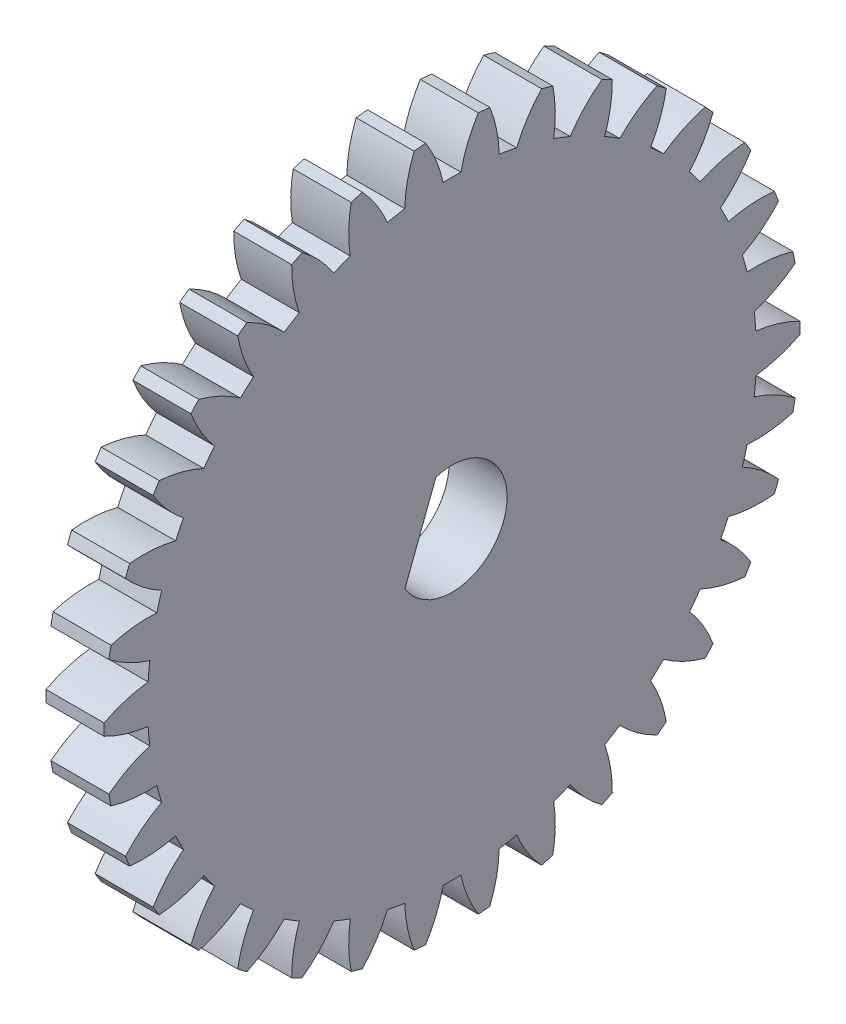
SolidWorks part; units mm, degrees
ref_plane "Plane1" through (0, 0, 0) normal (0, 0, 1) x (1, 0, 0)
ref_plane "Plane2" through (0, 0, 0) normal (0, 1, 0) x (1, 0, 0)
ref_plane "Plane3" through (0, 0, 0) normal (1, 0, 0) x (0, 0, -1)
sketch "HoldingSke" plane through (0, 0, 0) normal (0, 1, 0) x (1, 0, 0)
  line L0 (0, 0) -> (0.829, -0.5592)
  line L1 (-15, 0) -> (100, 0) construction
  line L2 (0, 0) -> (-2.1039, 2.3779)
  line L3 (0, 0) -> (-11.863, 4.5341)
  line L4 (0, 0) -> (7.1596, 4.8292)
  line L5 (0, 0) -> (-46.8476, -17.4728)
  line L6 (0, 0) -> (-2.4869, -1.6779)
  line L7 (-2.1039, 2.3779) -> (8.6586, 51.206)
  line L8 (-76.2, 54.61) -> (-75.7, 54.61)
  line L9 (-71.009, 38.7566) -> (-53.1078, 45.2721)
  line L10 (-76.2, 71.12) -> (104.1128, 71.12)
  line L11 (0, 0) -> (-3, 0)
  line L12 (-76.2, 101.6) -> (-76.162, 101.6)
  line L13 (24.9733, 27.94) -> (52.9518, 28.4284)
  line L14 (24.9733, 27.94) -> (24.9743, 27.94)
  line L15 (24.9733, 27.94) -> (100.4006, 29.5858)
  line L16 (-63.627, -1) -> (-12.827, -1)
  circle A0 centre (0, 0) radius 1.5
  circle A1 centre (0, 0) radius 15.749
  circle A2 centre (0, 0) radius 37.5
  circle A3 centre (0, 0) radius 1.5
  dimension "MHD" = 31.498
  dimension "Hub_dia" = 75
  dimension "Bore" = 3
  dimension "MBD" = 3
  dimension "Num_teeth" = 34
  dimension "Pitch" = 1
  dimension "Overall_len" = 50
  dimension "Show_teeth" = 34
  dimension "Thickness" = 3
  dimension "OAL" = 50.0002
  dimension "T_dim" = 0.5
  dimension "Ap" = 20
  dimension "H" = 19.05
  dimension "Pitch_radius" = 180.3128
  dimension "Width" = 3
  dimension "Backlash" = 0.038
  dimension "Addendum_fac" = 1
  dimension "Dedendum_fac" = 1.25
  dimension "Clearance_fac" = 0.25
  dimension "Dedendum_add" = 0.001
  dimension "Module" = 1
sketch "BasProSke" plane through (0, 0, 0) normal (0, 1, 0) x (1, 0, 0)
  line L0 (-10, 0) -> (60, 0) construction
  line L1 (0, 0) -> (0, 18)
  line L2 (0, 0) -> (3, 0)
  line L3 (3, 0) -> (3, 18)
  line L4 (3, 18) -> (0, 18)
  dimension "Thickness" = 3
  dimension "Diameter" = 36
revolve "Base-Revolve" add sketch "BasProSke" angle 360 about L0
sketch "TooCutSke" plane through (0, 0, 0) normal (1, 0, 0) x (0, 0, -1)
  line L1 (0, 0) -> (0, 107) construction
  line L2 (0, 0) -> (-0.8516, 16.9787) construction
  line L3 (0, 0) -> (-3.1343, 33.8247) construction
  line L4 (-0.8516, 16.9787) -> (-1.5672, 16.9124) construction
  arc A0 (0.4581, 15.7423) -> (-0.4581, 15.7423) centre (0, 0) ccw
  arc A1 (1.3773, 17.9727) -> (-1.3773, 17.9727) centre (0, 0) ccw
  circle A2 centre (0, 0) radius 17 construction
  circle A3 centre (0, 0) radius 15.9748 construction
  arc A4 (-0.4581, 15.7423) -> (-1.3773, 17.9727) centre (-7.1051, 14.3077) ccw
  arc A5 (1.3773, 17.9727) -> (0.4581, 15.7423) centre (7.1051, 14.3077) ccw
  dimension "Root_dia" = 31.498
  dimension "Overcut_dia" = 36.0508
  dimension "Pitch_dia" = 34
  dimension "Base_dia" = 31.9495
  dimension "Flank_rad" = 6.8
  dimension "Half_ang" = 5.294
  dimension "Half_CT" = 0.7186
extrude "ToothCut" cut sketch "TooCutSke" along normal through all
fillet "Breaks" [suppressed] radius 0.02
fillet "RootFillets" [suppressed] radius 0.251
pattern_circular "TeethCuts" count 34 every 10.588 about axis through (-10, 0, 0) along (1, 0, 0) of "ToothCut", "RootFillets", "Breaks"
sketch "HubNeaOneSke" plane through (0, 0, 0) normal (-1, 0, 0) x (0, 0, 1)
  circle A0 centre (0, 0) radius 15.749
  dimension "Diameter" = 31.498
extrude "HubNearOne" [suppressed] add sketch "HubNeaOneSke" along normal blind 47.0002
sketch "HubNeaBotSke" plane through (0, 0, 0) normal (-1, 0, 0) x (0, 0, 1)
  circle A0 centre (0, 0) radius 15.749
  dimension "Diameter" = 31.498
extrude "HubNearBoth" [suppressed] add sketch "HubNeaBotSke" along normal blind 23.5001
ref_plane "FarPln" through (3, 0, 0) normal (1, 0, 0) x (0, 0, -1)
sketch "HubFarSke" plane through (3, 0, 0) normal (1, 0, 0) x (0, 0, -1)
  circle A0 centre (0, 0) radius 15.749
  dimension "Diameter" = 31.498
extrude "HubFar" [suppressed] add sketch "HubFarSke" along normal blind 23.5001
sketch "KeySke" plane through (0, 0, 0) normal (1, 0, 0) x (0, 0, -1)
  line L0 (-0.6, 0) -> (-0.6, 2)
  line L1 (-0.6, 2) -> (0.6, 2)
  line L2 (0.6, 2) -> (0.6, 0)
  line L3 (0, 0) -> (0, 34) construction
  line L4 (-0.6, 0) -> (0.6, 0)
  dimension "Offset" = 2
  dimension "Width" = 1.2
extrude "Keyway" [suppressed] cut sketch "KeySke" along normal mid plane 100.0004
pattern_circular "Keyway2" [suppressed] count 2 every 90 about axis through (-10, 0, 0) along (1, 0, 0)
sketch "Sketch1" plane through (3, 0, 0) normal (1, 0, 0) x (0, 0, -1)
  line L0 (-0.8318, 2.7259) -> (-2.4367, -1.4782)
  arc A0 (-2.4367, -1.4782) -> (-0.8318, 2.7259) centre (0, 0) ccw
  dimension "D1" = 4.5
  dimension "D2" = 5.7
extrude "Cut-Extrude1" cut sketch "Sketch1" against normal through all
equation "' \"Module@HoldingSke\" = 6.35"
equation "' \"Num_teeth@HoldingSke\" = 12"
equation "' \"Ap@HoldingSke\" =  20"
equation "' \"Ap@HoldingSke\" = 20"
equation "' \"Width@HoldingSke\" = 0.5 * 25.4"
equation "' \"Hub_dia@HoldingSke\"= 1 * 25.4"
equation "' \"Hub_dia@HoldingSke\" = 1 * 25.4"
equation "' \"Overall_len@HoldingSke\" = 1.0 * 25.4"
equation "' \"Bore@HoldingSke\" = 0.75 * 25.4"
equation "' \"T_dim@HoldingSke\" = 0.1 * 25.4"
equation "' \"Width@KeySke\" = 0.25 * 25.4"
equation "' \"Show_teeth@HoldingSke\" = 13"
equation "' \"Backlash@HoldingSke\" = 0.009 * 25.4"
equation "' \"Dedendum_fac@HoldingSke\" = 1.25"
equation "' \"Dedendum_add@HoldingSke\" = 0.00005 * 25.4"
equation "' \"Clearance_fac@HoldingSke\" = 0.25"
equation "\"Pitch@HoldingSke\" = 1 / \"Module@HoldingSke\""
equation "\"Overcut_dia@TooCutSke\" = (\"Num_teeth@HoldingSke\" + 2 * \"Addendum_fac@HoldingSke\") / \"Pitch@HoldingSke\" + 0.002 * 25.4"
equation "\"Pitch_dia@TooCutSke\" = \"Num_teeth@HoldingSke\" / \"Pitch@HoldingSke\""
equation "\"Base_dia@TooCutSke\" = \"Num_teeth@HoldingSke\" / \"Pitch@HoldingSke\" * cos((\"Ap@HoldingSke\"  * 3.14159265 / 180))"
equation "\"Root_dia@TooCutSke\" = (\"Num_teeth@HoldingSke\" + 2) / \"Pitch@HoldingSke\" - 2 * (\"Addendum_fac@HoldingSke\" + \"Dedendum_fac@HoldingSke\") / \"Pitch@HoldingSke\" - \"Dedendum_add@HoldingSke\" * 2"
equation "\"Half_ang@TooCutSke\" = 180 / \"Num_teeth@HoldingSke\""
equation "\"Half_CT@TooCutSke\" = \"Num_teeth@HoldingSke\" / \"Pitch@HoldingSke\" * sin((3.14159265 / 2 / \"Num_teeth@HoldingSke\")) / 2 - 7 * \"Backlash@HoldingSke\" / 4"
equation "\"Flank_rad@TooCutSke\" = \"Num_teeth@HoldingSke\" / \"Pitch@HoldingSke\" / 5"
equation "\"Radius@RootFillets\" = \"Clearance_fac@HoldingSke\" / \"Pitch@HoldingSke\" + \"Dedendum_add@HoldingSke\""
equation "\"Break_rad@Breaks\" = 0.02 / \"Pitch@HoldingSke\""
equation "\"Thickness@HoldingSke\" = \"Width@HoldingSke\""
equation "\"OAL@HoldingSke\" = \"Thickness@HoldingSke\""
equation "\"MHD@HoldingSke\" = (\"Num_teeth@HoldingSke\" + 2) / \"Pitch@HoldingSke\" - 2 * (\"Addendum_fac@HoldingSke\" + \"Dedendum_fac@HoldingSke\")  / \"Pitch@HoldingSke\" - \"Dedendum_add@HoldingSke\" * 2"
equation "\"MBD@HoldingSke\" = (\"Num_teeth@HoldingSke\" + 2) / \"Pitch@HoldingSke\" - 2 * (\"Addendum_fac@HoldingSke\" + \"Dedendum_fac@HoldingSke\")  / \"Pitch@HoldingSke\" - \"Dedendum_add@HoldingSke\" * 2 - 0.002 * 25.4"
equation "\"MHD@HoldingSke\" = ((sgn( \"MHD@HoldingSke\" - \"Hub_dia@HoldingSke\" )-1)*( \"MHD@HoldingSke\" - \"Hub_dia@HoldingSke\" ))/-2+ \"Hub_dia@HoldingSke\""
equation "\"MBD@HoldingSke\" = ((sgn( \"MBD@HoldingSke\" - \"Bore@HoldingSke\" )-1)*( \"MBD@HoldingSke\" - \"Bore@HoldingSke\" ))/-2+ \"Bore@HoldingSke\""
equation "\"OAL@HoldingSke\" = ((sgn( \"OAL@HoldingSke\" - \"Overall_len@HoldingSke\" )+1)*( \"OAL@HoldingSke\" - \"Overall_len@HoldingSke\" ))/2 + \"Overall_len@HoldingSke\" + 0.000002 * 25.4"
equation "\"Num_teeth@TeethCuts\" = int( \"Show_teeth@HoldingSke\" ) + 1"
equation "\"Num_teeth@TeethCuts\" = ((sgn( \"Num_teeth@TeethCuts\" - \"Num_teeth@HoldingSke\" )-1)*( \"Num_teeth@TeethCuts\" - \"Num_teeth@HoldingSke\" ))/-2+ \"Num_teeth@HoldingSke\""
equation "\"Num_teeth@TeethCuts\" = ((sgn( \"Num_teeth@TeethCuts\" - 2.0)+1)*( \"Num_teeth@TeethCuts\" - 2.0))/2 +2.0"
equation "\"Angle@TeethCuts\" = 360.0 / \"Num_teeth@HoldingSke\""
equation "\"Diameter@BasProSke\" = (\"Num_teeth@HoldingSke\" + 2 * \"Addendum_fac@HoldingSke\") / \"Pitch@HoldingSke\""
equation "\"Thickness@BasProSke\"  = \"Thickness@HoldingSke\""
equation "' \"Fillet_rad@BasProSke\" =  \"Thickness@HoldingSke\" * 0.05"
equation "' \"Fillet_rad@BasProSke\" = \"Thickness@HoldingSke\" * 0.05"
equation "\"MHD@HoldingSke\" = ((sgn( \"MHD@HoldingSke\" - \"Root_dia@TooCutSke\" )-1)*( \"MHD@HoldingSke\" - \"Root_dia@TooCutSke\" ))/-2+ \"Root_dia@TooCutSke\""
equation "\"Diameter@HubNeaOneSke\" = \"MHD@HoldingSke\""
equation "\"Length@HubNearOne\" = \"OAL@HoldingSke\" - \"Thickness@BasProSke\""
equation "\"Diameter@HubNeaBotSke\" = \"MHD@HoldingSke\""
equation "\"Length@HubNearBoth\" = ( \"OAL@HoldingSke\" - \"Thickness@BasProSke\" ) / 2.0"
equation "\"Thickness@FarPln\" = \"Thickness@BasProSke\""
equation "\"Diameter@HubFarSke\" = \"MHD@HoldingSke\""
equation "\"Length@HubFar\" = ( \"OAL@HoldingSke\" - \"Thickness@BasProSke\" ) / 2.0"
equation "\"D1\"= \"OAL@HoldingSke\" * 2.0"
equation "\"D1@Keyway\" = \"OAL@HoldingSke\" * 2.0"
equation "\"Offset@KeySke\" = \"T_dim@HoldingSke\" + \"MBD@HoldingSke\" / 2.0"
